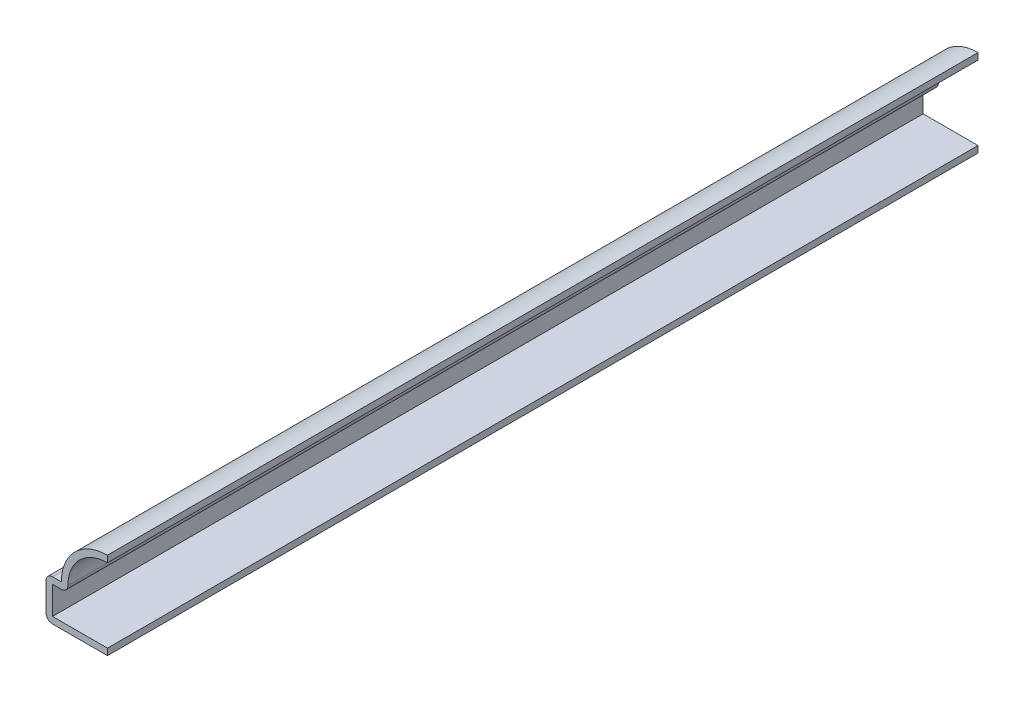
SolidWorks part; units mm, degrees
ref_plane "Front Plane" through (0, 0, 0) normal (0, 0, 1) x (1, 0, 0)
ref_plane "Top Plane" through (0, 0, 0) normal (0, 1, 0) x (1, 0, 0)
ref_plane "Right Plane" through (0, 0, 0) normal (1, 0, 0) x (0, 0, -1)
sketch "Sketch1" plane through (0, 0, 0) normal (0, 0, 1) x (1, 0, 0)
  line L0 (0, 0) -> (-9.525, 0)
  line L1 (-9.525, 0) -> (-9.525, 6.35)
  line L2 (-9.525, 6.35) -> (-7.1438, 6.35)
  arc A0 (-7.1438, 6.35) -> (0, 13.4937) centre (0, 6.35) cw
  point P7 (0, 0)
  dimension "D5" = 7.1437
  dimension "D1" = 9.525
  dimension "D2" = 6.35
  dimension "D3" = 2.3813
  dimension "D4" = 13.4937
extrude "Extrude-Thin1" add sketch "Sketch1" against normal blind 134.9375 thin
fillet "Fillet1" radius 1.016 3 edges at (-9.525, 0, -67.4688) (-9.525, 6.35, -67.4688) (-6.0429, 5.334, -67.4688)
